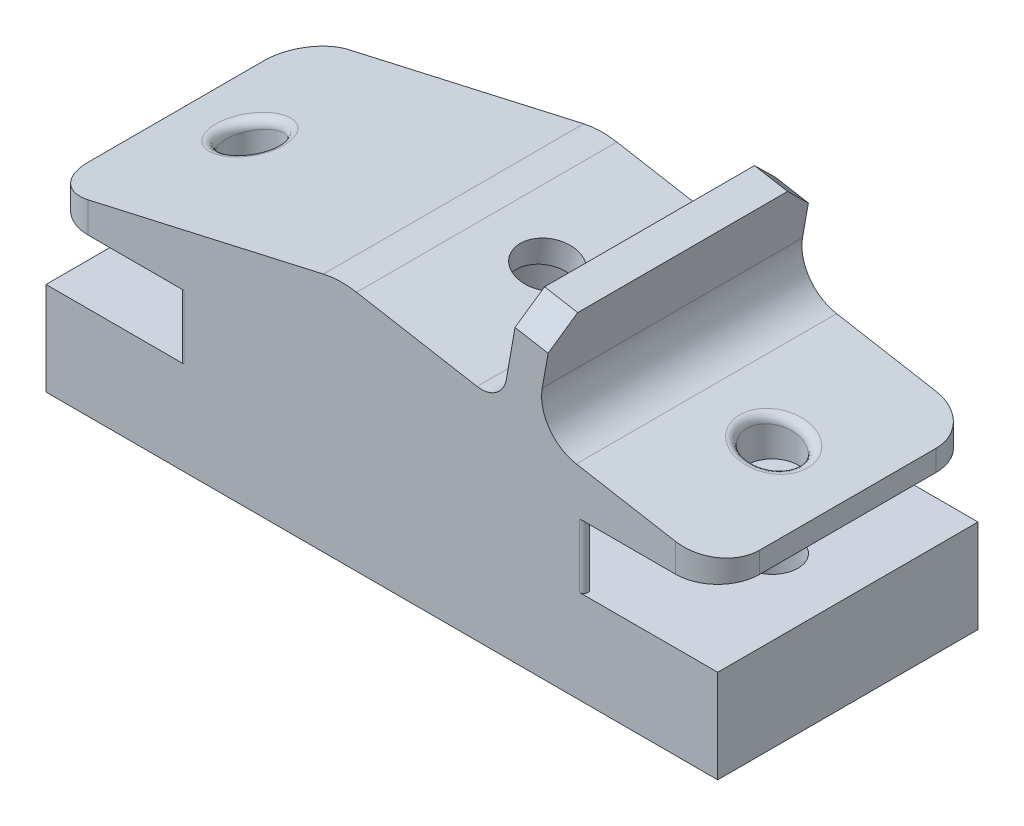
SolidWorks part; units mm, degrees
ref_plane "Front Plane" through (0, 0, 0) normal (0, 0, 1) x (1, 0, 0)
ref_plane "Top Plane" through (0, 0, 0) normal (0, 1, 0) x (1, 0, 0)
ref_plane "Right Plane" through (0, 0, 0) normal (1, 0, 0) x (0, 0, -1)
sketch "Sketch1" plane through (0, 0, 0) normal (0, 1, 0) x (1, 0, 0)
  line L0 (-40, 0) -> (40, 0) construction
  line L1 (40, -15.5) -> (-40, -15.5)
  line L2 (40, -15.5) -> (40, 15.5)
  line L3 (40, 15.5) -> (-40, 15.5)
  line L4 (-40, -15.5) -> (-40, 15.5)
  line L5 (40, -15.5) -> (-40, 15.5) construction
  line L6 (40, 15.5) -> (-40, -15.5) construction
  line L7 (-31, 0) -> (0, 15.5) construction
  line L8 (0, 15.5) -> (31, 0) construction
  circle A0 centre (-31, 0) radius 6
  circle A1 centre (31, 0) radius 6
  point P0 (0, 0)
  dimension "D3" = 12
  dimension "D1" = 80
  dimension "D2" = 31
  dimension "D4" = 62
extrude "Boss-Extrude1" add sketch "Sketch1" along normal blind 6
sketch "Sketch2" plane through (0, 6, 0) normal (0, 1, 0) x (1, 0, 0)
  line L4 (-40, 15.5) -> (-40, -15.5)
  line L5 (-40, -15.5) -> (40, -15.5)
  line L6 (40, -15.5) -> (40, 15.5)
  line L7 (40, 15.5) -> (-40, 15.5)
  line L8 (-40, 15.5) -> (-40, -15.5)
  line L9 (-40, -15.5) -> (40, -15.5)
  line L10 (40, -15.5) -> (40, 15.5)
  line L11 (40, 15.5) -> (-40, 15.5)
  circle A0 centre (-31, 0) radius 3.05
  circle A1 centre (31, 0) radius 3.05
  dimension "D2" = 6.1
  dimension "D1" = 0
extrude "Boss-Extrude2" add sketch "Sketch2" along normal blind 5.9
sketch "Sketch3" plane through (0, 11.9, 0) normal (0, 1, 0) x (1, 0, 0)
  line L0 (40, 15.5) -> (-40, 15.5) construction
  line L1 (40, 15.5) -> (-40, 15.5)
  line L2 (-40, -15.5) -> (40, -15.5) construction
  line L3 (-40, -15.5) -> (40, -15.5)
  circle A0 centre (-31, 0) radius 16.25
  circle A1 centre (31, 0) radius 16.25
  line M3 (40, 15.5) -> (-40, 15.5)
  line M5 (-40, -15.5) -> (40, -15.5)
  dimension "D1" = 32.5
extrude "Boss-Extrude3" add sketch "Sketch3" along normal blind 6.8 contours A1 A0 M3 M5
fillet "Fillet1" radius 0.5 4 edges at (26.1202, 15.3, -15.5) (26.1202, 15.3, 15.5) (-26.1202, 15.3, 15.5) (-26.1202, 15.3, -15.5)
sketch "Sketch4" plane through (0, 18.7, 0) normal (0, 1, 0) x (1, 0, 0)
  line L1 (-40, 15.5) -> (40, 15.5)
  line L2 (-40, 15.5) -> (-40, -15.5)
  line L3 (-40, -15.5) -> (40, -15.5)
  line L4 (40, 15.5) -> (40, -15.5)
  circle A0 centre (-31, 0) radius 3.05 construction
  circle A1 centre (-31, 0) radius 3.05
  circle A2 centre (31, 0) radius 3.05 construction
  circle A3 centre (31, 0) radius 3.05
extrude "Boss-Extrude4" add sketch "Sketch4" along normal blind 2.5
sketch "Sketch5" plane through (0, 0, 15.5) normal (0, 0, 1) x (1, 0, 0)
  line L0 (40, 21.2) -> (-5, 29.1347)
  line L1 (-5, 29.1347) -> (-40, 21.2)
  line L2 (-40, 21.2) -> (40, 21.2)
  dimension "D1" = 10
  dimension "D2" = 35
extrude "Boss-Extrude5" add sketch "Sketch5" against normal up to surface (31 mm away) up to face at (0, 13.7333, -15.5)
sketch "Sketch6" plane through (4.8316, 27.4011, 0) normal (0.1736, 0.9848, 0) x (0.9848, -0.1736, 0)
  line L0 (-9.9832, 0) -> (39.3923, 0) construction
  line L1 (-9.9832, 15.5) -> (-9.9832, -15.5) construction
  line L2 (39.3923, -15.5) -> (39.3923, 15.5) construction
  circle A0 centre (-0.6077, 0) radius 3.3
  dimension "D1" = 6.6
  dimension "D2" = 40
extrude "Cut-Extrude1" cut sketch "Sketch6" against normal blind 48
ref_plane "Plane1" through (-3.8508, -21.8392, 0) normal (0.1736, 0.9848, 0) x (0.9848, -0.1736, 0)
sketch "Sketch7" plane through (-3.8508, -21.8392, 0) normal (0.1736, 0.9848, 0) x (0.9848, -0.1736, 0)
  circle A0 centre (-0.6077, 0) radius 7.8
  dimension "D1" = 15.6
extrude "Cut-Extrude2" cut sketch "Sketch7" along normal offset from surface (47 mm away) 3 up to face at (0.9832, 28.0797, 0)
sketch "Sketch8" plane through (0, 0, 15.5) normal (0, 0, 1) x (1, 0, 0)
  line L0 (14.2965, 25.7322) -> (16.3803, 37.5499)
  line L1 (40, 21.2) -> (-5, 29.1347) construction
  line L2 (16.3803, 37.5499) -> (20.3195, 36.8553)
  line L3 (20.3195, 36.8553) -> (18.2357, 25.0376)
  line L4 (18.2357, 25.0376) -> (14.2965, 25.7322)
  dimension "D1" = 4
  dimension "D2" = 12
  dimension "D3" = 22.1
extrude "Boss-Extrude6" add sketch "Sketch8" against normal up to surface (31 mm away) up to face at (-0.3846, 14.9181, -15.5)
fillet "Fillet2" radius 3 1 edges at (14.2965, 25.7322, 0)
fillet "Fillet3" radius 5 1 edges at (18.2357, 25.0376, 0)
chamfer "Chamfer1" distance 3 angle 45 2 edges at (18.3499, 37.2026, -15.5) (18.3499, 37.2026, 15.5)
fillet "Fillet4" radius 5 4 edges at (40, 19.95, -15.5) (40, 19.95, 15.5) (-40, 19.95, -15.5) (-40, 19.95, 15.5)
fillet "Fillet5" radius 10 1 edges at (-5, 29.1347, 0)
sketch "Sketch9" plane through (0, 6, 0) normal (0, -1, 0) x (1, 0, 0)
  circle A0 centre (-31, 0) radius 3.05 construction
  circle A1 centre (-31, 0) radius 3.05
  circle A2 centre (31, 0) radius 3.05 construction
  circle A3 centre (31, 0) radius 3.05
extrude "Cut-Extrude3" cut sketch "Sketch9" against normal through all
fillet "Fillet6" radius 1 2 edges at (34.05, 22.2491, 0) (-34.05, 22.5489, 0)
sketch "Sketch10" plane through (0, 11.9, 0) normal (0, 1, 0) x (1, 0, 0)
  line L3 (40, 15.5) -> (23.546, 15.5)
  line L4 (23.546, -15.5) -> (40, -15.5)
  line L5 (40, -15.5) -> (40, 15.5)
  line L6 (40, 15.5) -> (23.546, 15.5)
  line L7 (23.546, -15.5) -> (40, -15.5)
  line L8 (40, -15.5) -> (40, 15.5)
  line L9 (-40, -15.5) -> (-23.546, -15.5)
  line L10 (-23.546, 15.5) -> (-40, 15.5)
  line L11 (-40, 15.5) -> (-40, -15.5)
  line L12 (-40, -15.5) -> (-23.546, -15.5)
  line L13 (-23.546, 15.5) -> (-40, 15.5)
  line L14 (-40, 15.5) -> (-40, -15.5)
  arc A3 (23.7685, 14.5522) -> (23.546, 15.5) centre (23.546, 15) ccw
  arc A4 (23.7685, 14.5522) -> (23.7685, -14.5522) centre (31, 0) ccw
  arc A5 (23.546, -15.5) -> (23.7685, -14.5522) centre (23.546, -15) ccw
  arc A6 (23.7685, 14.5522) -> (23.546, 15.5) centre (23.546, 15) ccw
  arc A7 (23.7685, 14.5522) -> (23.7685, -14.5522) centre (31, 0) ccw
  arc A8 (23.546, -15.5) -> (23.7685, -14.5522) centre (23.546, -15) ccw
  arc A9 (-23.7685, -14.5522) -> (-23.546, -15.5) centre (-23.546, -15) ccw
  arc A10 (-23.7685, -14.5522) -> (-23.7685, 14.5522) centre (-31, 0) ccw
  arc A11 (-23.546, 15.5) -> (-23.7685, 14.5522) centre (-23.546, 15) ccw
  arc A12 (-23.7685, -14.5522) -> (-23.546, -15.5) centre (-23.546, -15) ccw
  arc A13 (-23.7685, -14.5522) -> (-23.7685, 14.5522) centre (-31, 0) ccw
  arc A14 (-23.546, 15.5) -> (-23.7685, 14.5522) centre (-23.546, 15) ccw
  dimension "D1" = 0
  dimension "D2" = 0
extrude "Cut-Extrude4" cut sketch "Sketch10" against normal blind 0.8
